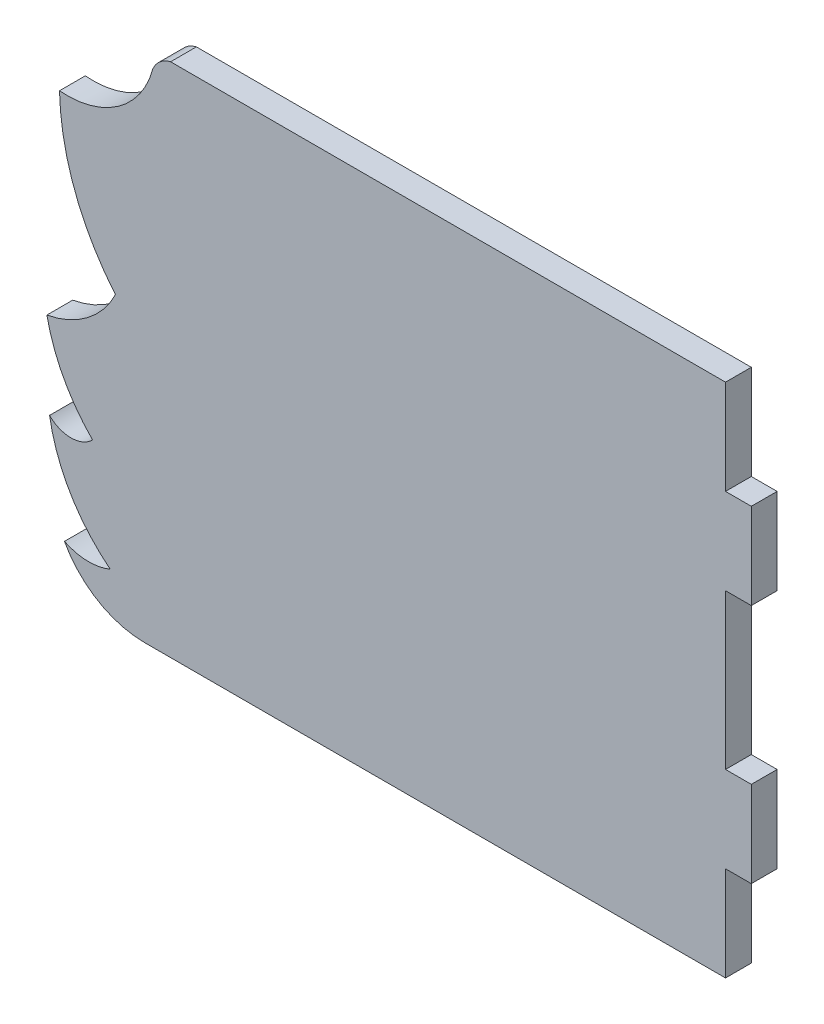
SolidWorks part; units mm, degrees
ref_plane "Alzado" through (0, 0, 0) normal (0, 0, 1) x (1, 0, 0)
ref_plane "Planta" through (0, 0, 0) normal (0, 1, 0) x (1, 0, 0)
ref_plane "Vista lateral" through (0, 0, 0) normal (1, 0, 0) x (0, 0, -1)
sketch "Model" plane through (0, 0, 0) normal (0, 0, 1) x (1, 0, 0)
  line L0 (96.7858, 36.0158) -> (93.7858, 36.0158)
  line L1 (93.7858, 36.0158) -> (93.7858, 47.0158)
  line L2 (93.7858, 47.0158) -> (31.7512, 47.0158)
  line L3 (31.7512, 47.0158) -> (29.2607, 47.0158)
  line L4 (26.2607, -12.9842) -> (36.4111, -12.9842)
  line L5 (96.7858, 26.0158) -> (96.7858, 36.0158)
  line L6 (96.7858, 8.0158) -> (93.7858, 8.0158)
  line L7 (93.7858, 8.0158) -> (93.7858, 26.0158)
  line L8 (93.7858, 26.0158) -> (96.7858, 26.0158)
  line L9 (36.4111, -12.9842) -> (93.7858, -12.9842)
  line L10 (93.7858, -12.9842) -> (93.7858, -1.9842)
  line L11 (93.7858, -1.9842) -> (96.7858, -1.9842)
  line L12 (96.7858, 8.0158) -> (96.7858, -1.9842)
  arc A0 (29.2607, 47.0158) -> (27.1935, 45.2574) centre (29.9607, 44.0986) ccw
  arc A1 (16.3428, 37.6386) -> (27.1935, 45.2574) centre (17.2324, 47.9079) ccw
  arc A2 (16.3428, 37.6386) -> (22.8506, 20.358) centre (44.2662, 38.2887) ccw
  arc A3 (14.8783, 14.3212) -> (22.8506, 20.358) centre (12.8277, 25.3119) ccw
  arc A4 (14.8783, 14.3212) -> (20.1883, 4.3957) centre (34.273, 18.3138) ccw
  arc A5 (15.1883, 4.3726) -> (20.1883, 4.3957) centre (17.6768, 6.8841) ccw
  arc A6 (15.1883, 4.3726) -> (22.2436, -7.595) centre (34.2738, 7.5606) ccw
  arc A7 (16.9209, -7.448) -> (22.2436, -7.595) centre (19.7465, -1.573) ccw
  arc A8 (16.9209, -7.448) -> (26.2607, -12.9842) centre (26.2596, -2.3395) ccw
extrude "Saliente-Extruir1" add sketch "Model" along normal blind 3
